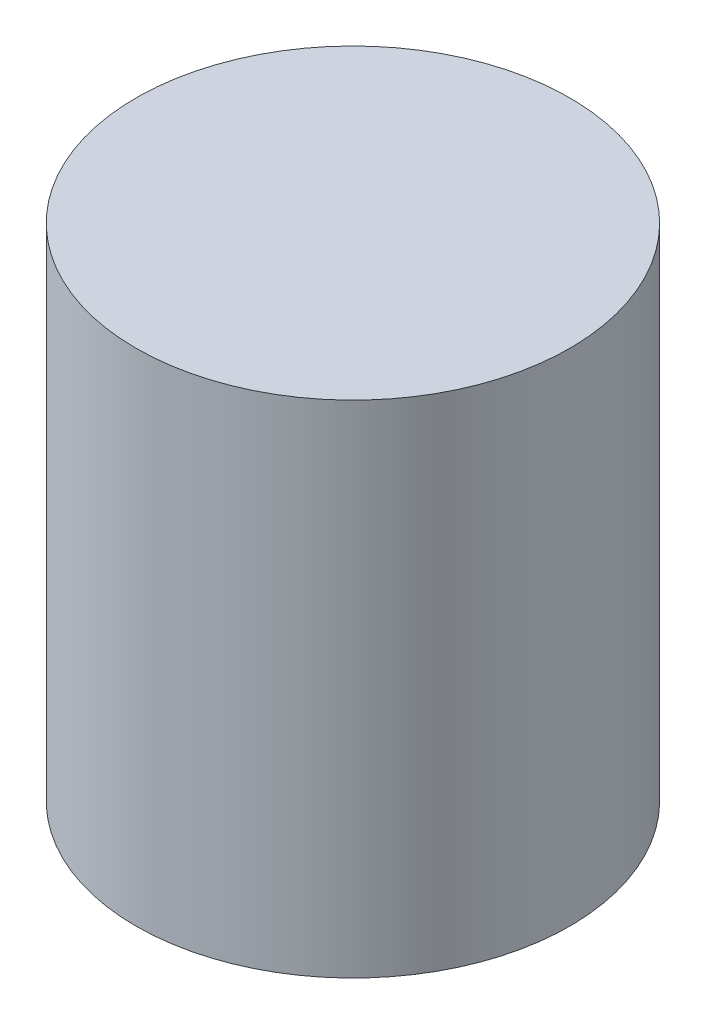
SolidWorks part; units mm, degrees
ref_plane "Front Plane" through (0, 0, 0) normal (0, 0, 1) x (1, 0, 0)
ref_plane "Top Plane" through (0, 0, 0) normal (0, 1, 0) x (1, 0, 0)
ref_plane "Right Plane" through (0, 0, 0) normal (1, 0, 0) x (0, 0, -1)
sketch "Sketch1" plane through (0, 0, 0) normal (0, 1, 0) x (1, 0, 0)
  circle A0 centre (0, 0) radius 6.5
  dimension "D1" = 13
extrude "Boss-Extrude1" add sketch "Sketch1" along normal blind 15
sketch "Sketch2" plane through (0, 0, 0) normal (0, -1, 0) x (1, 0, 0)
  circle A0 centre (0, 0) radius 3
  dimension "D1" = 6
extrude "Cut-Extrude1" cut sketch "Sketch2" against normal blind 10
